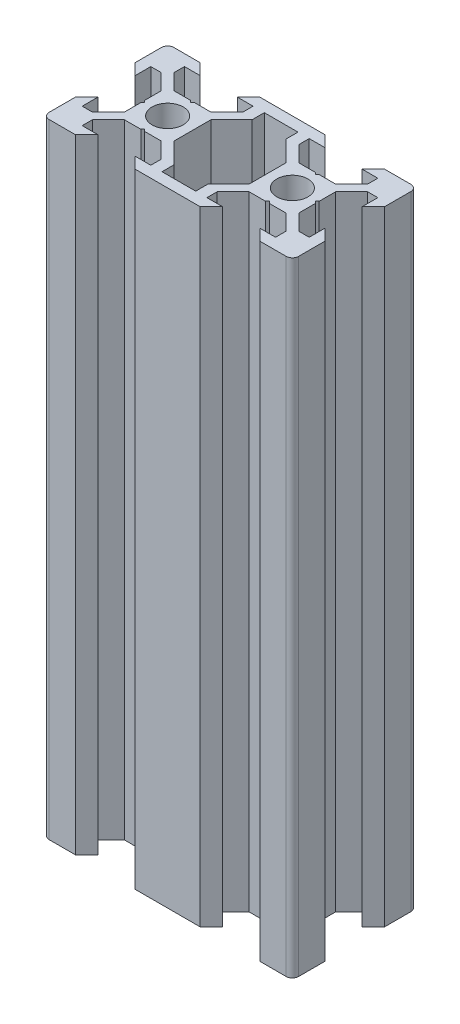
SolidWorks part; units mm, degrees
material "6063-T5"
ref_plane "Plano frontal" through (0, 0, 0) normal (0, 0, 1) x (1, 0, 0)
ref_plane "Plano superior" through (0, 0, 0) normal (0, 1, 0) x (1, 0, 0)
ref_plane "Plano direito" through (0, 0, 0) normal (1, 0, 0) x (0, 0, -1)
sketch "Esboço1" plane through (0, 0, 0) normal (0, 0, 1) x (1, 0, 0)
  line L0 (0, 0) -> (0, 100)
  dimension "D1" = 100
other "Retangular PF20-12 - PERFIL 2040 V-SLOT(1)"
ref_plane "Plano1" through (0, 0, 0) normal (0, 1, 0) x (-1, 0, 0)
sketch "Sketch13" plane through (0, 0, 0) normal (0, 1, 0) x (-1, 0, 0)
  line L0 (-14.8, 10) -> (-13, 8.2)
  line L1 (-13, 8.2) -> (-15.5, 8.2)
  line L2 (-15.5, 8.2) -> (-15.5, 6.5607)
  line L3 (-15.5, 6.5607) -> (-12.9393, 4)
  line L4 (-12.9393, 4) -> (-10.3, 4)
  line L5 (-4.5, 6.5607) -> (-7.0607, 4)
  line L6 (-4.5, 8.2) -> (-4.5, 6.5607)
  line L7 (-7, 8.2) -> (-4.5, 8.2)
  line L8 (-5.2, 10) -> (-7, 8.2)
  line L9 (-10.3, 4) -> (-10, 3.7)
  line L10 (-9.7, 4) -> (-10, 3.7)
  line L11 (-9.7, 4) -> (-7.0607, 4)
  line L12 (-2.7, 8.2) -> (-2.7, 6.2393)
  line L13 (-2.7, 6.2393) -> (-6, 2.9393)
  line L14 (-2.7, 8.2) -> (2.7, 8.2)
  line L15 (2.7, 6.2393) -> (6, 2.9393)
  line L16 (2.7, 8.2) -> (2.7, 6.2393)
  line L17 (-5.2, -10) -> (5.2, -10)
  line L18 (-5.2, -10) -> (-7, -8.2)
  line L19 (-7, -8.2) -> (-4.5, -8.2)
  line L20 (-4.5, -8.2) -> (-4.5, -6.5607)
  line L21 (-4.5, -6.5607) -> (-7.0607, -4)
  line L22 (-7.0607, -4) -> (-9.7, -4)
  line L23 (-9.7, -4) -> (-10, -3.7)
  line L24 (-10.3, -4) -> (-10, -3.7)
  line L25 (-10.3, -4) -> (-12.9393, -4)
  line L26 (-15.5, -6.5607) -> (-12.9393, -4)
  line L27 (-15.5, -8.2) -> (-15.5, -6.5607)
  line L28 (-13, -8.2) -> (-15.5, -8.2)
  line L29 (-14.8, -10) -> (-13, -8.2)
  line L30 (-20, -4.8) -> (-20, -9)
  line L31 (-20, -4.8) -> (-18.2, -3)
  line L32 (-18.2, -3) -> (-18.2, -5.5)
  line L33 (-18.2, -5.5) -> (-16.5607, -5.5)
  line L34 (-16.5607, -5.5) -> (-14, -2.9393)
  line L35 (-14, -2.9393) -> (-14, -0.3)
  line L36 (-14, -0.3) -> (-13.7, 0)
  line L37 (-14, 0.3) -> (-13.7, 0)
  line L38 (-14, 0.3) -> (-14, 2.9393)
  line L39 (-16.5607, 5.5) -> (-14, 2.9393)
  line L40 (-18.2, 5.5) -> (-16.5607, 5.5)
  line L41 (-18.2, 3) -> (-18.2, 5.5)
  line L42 (-20, 4.8) -> (-18.2, 3)
  line L43 (-14.8, 10) -> (-19, 10)
  line L56 (5.2, 10) -> (-5.2, 10)
  line L57 (5.2, 10) -> (7, 8.2)
  line L58 (7, 8.2) -> (4.5, 8.2)
  line L59 (4.5, 8.2) -> (4.5, 6.5607)
  line L60 (4.5, 6.5607) -> (7.0607, 4)
  line L61 (9.7, 4) -> (7.0607, 4)
  line L62 (9.7, 4) -> (10, 3.7)
  line L63 (10.3, 4) -> (10, 3.7)
  line L64 (12.9393, 4) -> (10.3, 4)
  line L65 (15.5, 6.5607) -> (12.9393, 4)
  line L66 (15.5, 8.2) -> (15.5, 6.5607)
  line L67 (13, 8.2) -> (15.5, 8.2)
  line L68 (14.8, 10) -> (13, 8.2)
  line L69 (20, 4.8) -> (18.2, 3)
  line L70 (18.2, 3) -> (18.2, 5.5)
  line L71 (18.2, 5.5) -> (16.5607, 5.5)
  line L72 (16.5607, 5.5) -> (14, 2.9393)
  line L73 (14, 0.3) -> (14, 2.9393)
  line L74 (14, 0.3) -> (13.7, 0)
  line L75 (14, -0.3) -> (13.7, 0)
  line L76 (14, -2.9393) -> (14, -0.3)
  line L77 (16.5607, -5.5) -> (14, -2.9393)
  line L78 (18.2, -5.5) -> (16.5607, -5.5)
  line L79 (18.2, -3) -> (18.2, -5.5)
  line L80 (20, -4.8) -> (18.2, -3)
  line L81 (20, -9) -> (20, -4.8)
  line L82 (14.8, -10) -> (13, -8.2)
  line L83 (13, -8.2) -> (15.5, -8.2)
  line L84 (15.5, -8.2) -> (15.5, -6.5607)
  line L85 (15.5, -6.5607) -> (12.9393, -4)
  line L86 (10.3, -4) -> (12.9393, -4)
  line L87 (10.3, -4) -> (10, -3.7)
  line L88 (9.7, -4) -> (10, -3.7)
  line L89 (7.0607, -4) -> (9.7, -4)
  line L90 (4.5, -6.5607) -> (7.0607, -4)
  line L91 (4.5, -8.2) -> (4.5, -6.5607)
  line L92 (7, -8.2) -> (4.5, -8.2)
  line L93 (5.2, -10) -> (7, -8.2)
  line L99 (-6, 2.9393) -> (-6, -2.9393)
  line L100 (-2.7, -6.2393) -> (-6, -2.9393)
  line L101 (-2.7, -8.2) -> (-2.7, -6.2393)
  line L102 (-2.7, -8.2) -> (2.7, -8.2)
  line L103 (2.7, -8.2) -> (2.7, -6.2393)
  line L104 (2.7, -6.2393) -> (6, -2.9393)
  line L105 (6, 2.9393) -> (6, -2.9393)
  line L106 (-20, 9) -> (-20, 4.8)
  line L107 (-19, -10) -> (-14.8, -10)
  line L108 (19, 10) -> (14.8, 10)
  line L109 (20, 4.8) -> (20, 9)
  line L110 (14.8, -10) -> (19, -10)
  arc A3 (-20, -9) -> (-19, -10) centre (-19, -9) ccw
  arc A4 (-19, 10) -> (-20, 9) centre (-19, 9) ccw
  arc A5 (20, 9) -> (19, 10) centre (19, 9) ccw
  arc A6 (19, -10) -> (20, -9) centre (19, -9) ccw
  circle A7 centre (-10, 0) radius 2.5
  circle A8 centre (10, 0) radius 2.5
  point P1 (-20, 10)
  point P2 (20, 10)
  point P4 (20, 0)
  point P108 (0, 10)
  point P109 (0, 0)
  point P111 (20, -10)
  point P112 (10, -10)
  point P113 (-10, -10)
  point P114 (-20, -10)
  point P115 (-20, 0)
  point P116 (-10, 10)
  point P117 (10, 10)
  point P118 (-10, 0)
  point P119 (10, 0)
  point P120 (0, -10)
  point P121 (0, 0)
